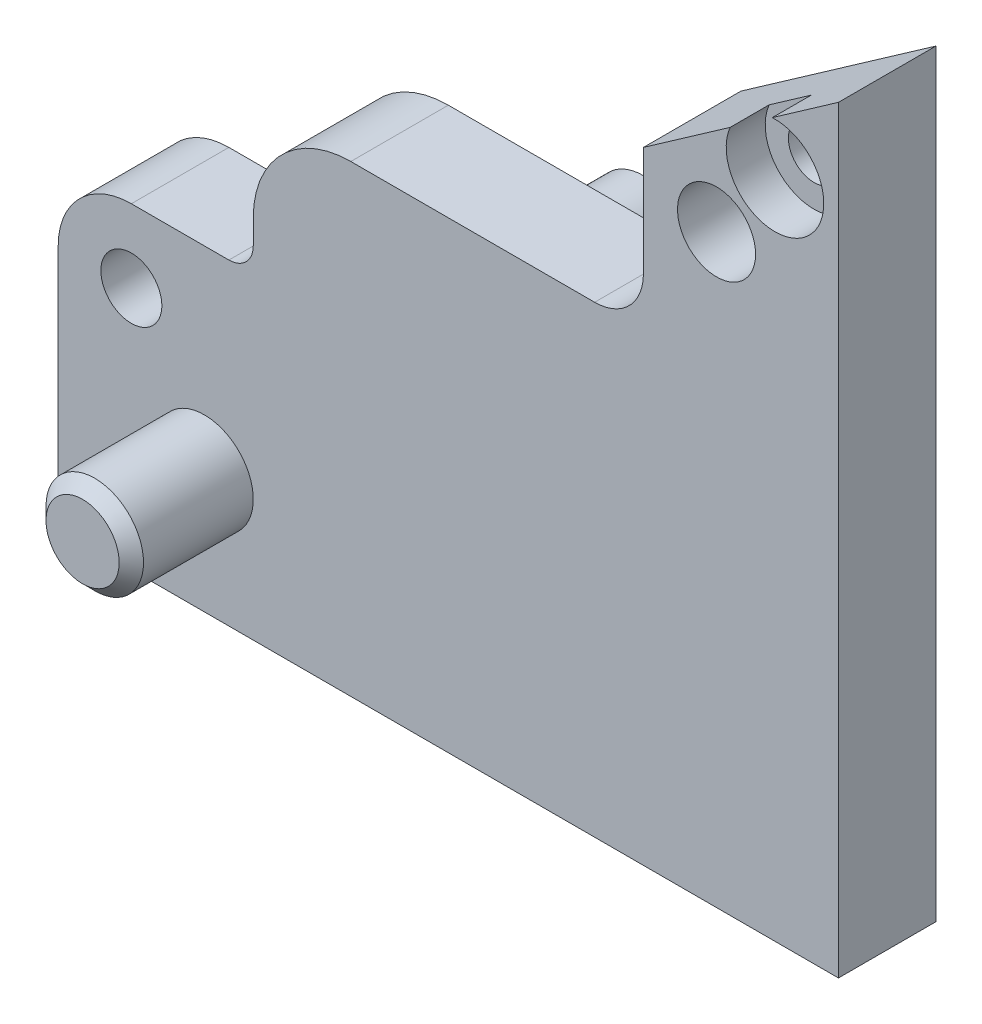
SolidWorks part; units mm, degrees
ref_plane "Front Plane" through (0, 0, 0) normal (0, 0, 1) x (1, 0, 0)
ref_plane "Top Plane" through (0, 0, 0) normal (0, 1, 0) x (1, 0, 0)
ref_plane "Right Plane" through (0, 0, 0) normal (1, 0, 0) x (0, 0, -1)
ref_plane "Plane1" through (0, 0, 0) normal (0, 0, -1) x (-1, 0, 0)
sketch "Sketch1" plane through (0, 0, 0) normal (0, 0, -1) x (-1, 0, 0)
  line L0 (0, 0) -> (0, 31.1017)
  line L1 (0, 31.1017) -> (-32, 31.1017)
  line L2 (-32, 31.1017) -> (-32, 0)
  line L3 (-32, 0) -> (0, 0)
extrude "Boss-Extrude1" add sketch "Sketch1" against normal blind 4
sketch "Sketch2" plane through (0, 0, 4) normal (0, 0, 1) x (1, 0, 0)
  line L0 (0, 13) -> (8, 13)
  line L1 (8, 13) -> (8, 31.1017)
  line L2 (8, 31.1017) -> (0, 31.1017)
  line L3 (0, 31.1017) -> (0, 13)
extrude "Cut-Extrude1" cut sketch "Sketch2" against normal through all
sketch "Sketch3" plane through (0, 0, 4) normal (0, 0, 1) x (1, 0, 0)
  line L0 (8, 19) -> (24, 19)
  line L1 (24, 19) -> (24, 31.1017)
  line L2 (24, 31.1017) -> (8, 31.1017)
  line L3 (8, 31.1017) -> (8, 19)
extrude "Cut-Extrude2" cut sketch "Sketch3" against normal through all
draft "Draft1" type of draft neutral plane draft angle 35 faces to draft 1 face at (28, 31.1017, 2) neutral plane through (32, 31.1017, 4) neutral plane normal (1, 0, 0) reverse direction yes parameters "D1"=35
ref_plane "Plane2" through (0, 5, 0) normal (0, -1, 0) x (1, 0, 0)
sketch "Sketch4" plane through (0, 5, 0) normal (0, -1, 0) x (1, 0, 0)
  line L0 (8, 9) -> (6, 9)
  line L1 (6, 9) -> (6, 4)
  line L2 (6, 4) -> (8, 4)
  line L3 (8, 4) -> (8, 9)
  line L4 (6, 9) -> (6, 4) construction
revolve "Revolve1" add sketch "Sketch4" angle 360 about L4
ref_plane "Plane3" through (0, 14, 0) normal (0, 1, 0) x (1, 0, 0)
sketch "Sketch5" plane through (0, 14, 0) normal (0, 1, 0) x (1, 0, 0)
  line L0 (17.5, 5) -> (15.5, 5)
  line L1 (15.5, 5) -> (15.5, 0)
  line L2 (15.5, 0) -> (17.5, 0)
  line L3 (17.5, 0) -> (17.5, 5)
  line L4 (15.5, 5) -> (15.5, 0) construction
revolve "Revolve2" add sketch "Sketch5" angle 360 about L4
hole_wizard "Ø3.2 (3.2) Diameter Hole1" positions "Sketch7" profile "Sketch6" hole size "Ø3.2" standard "ANSI Metric"
sketch "Sketch7" plane through (0, 0, 4) normal (0, 0, 1) x (1, 0, 0)
  point P0 (27, 24)
sketch "Sketch6" plane through (27, 24, 4) normal (1, 0, 0) x (0, -1, 0)
  line L0 (0, 0) -> (0, 9)
  line L1 (0, 9) -> (1.6, 9)
  line L2 (1.6, 9) -> (1.6, 0)
  line L5 (1.6, 0) -> (0, 0)
  line L11 (0, -6.35) -> (0, 107.95) construction
  dimension "Thru Hole Dia." = 3.2
  dimension "Thru Hole Depth" = 9
hole_wizard "Ø2.5 (2.5) Diameter Hole1" positions "Sketch9" profile "Sketch8" hole size "Ø2.5" standard "ANSI Metric"
sketch "Sketch9" plane through (0, 0, 0) normal (0, 0, -1) x (-1, 0, 0)
  point P0 (-3, 10)
sketch "Sketch8" plane through (3, 10, 0) normal (1, 0, 0) x (0, 1, 0)
  line L0 (0, 0) -> (0, 9)
  line L1 (0, 9) -> (1.25, 9)
  line L2 (1.25, 9) -> (1.25, 0)
  line L5 (1.25, 0) -> (0, 0)
  line L11 (0, -6.35) -> (0, 107.95) construction
  dimension "Thru Hole Dia." = 2.5
  dimension "Thru Hole Depth" = 9
hole_wizard "M4x0.7 Tapped Hole1" positions "Sketch11" profile "Sketch10" tap size "M4x0.7" standard "ANSI Metric"
sketch "Sketch11" plane through (0, 0, 4) normal (0, 0, 1) x (1, 0, 0)
  point P0 (29.396, 27.203)
sketch "Sketch10" plane through (29.396, 27.203, 4) normal (1, 0, 0) x (0, -1, 0)
  line L0 (0, 0) -> (0, 9)
  line L1 (0, 9) -> (1.05, 9)
  line L3 (1.05, 9) -> (1.05, 1.6)
  line L4 (1.05, 1.6) -> (2, 1.6)
  line L5 (2, 1.6) -> (2, 0)
  line L7 (2, 0) -> (0, 0)
  line L11 (0, -6.35) -> (0, 107.95) construction
  dimension "Thru Tap Drill Dia." = 2.1
  dimension "Thru Tap Drill Depth" = 9
  dimension "Thread Major Dia." = 4
  dimension "Thread Depth" = 1.6
hole_wizard "Ø2.5 (2.5) Diameter Hole2" positions "Sketch13" profile "Sketch12" hole size "Ø2.5" standard "ANSI Metric"
sketch "Sketch13" plane through (0, 0, 0) normal (0, -1, 0) x (-1, 0, 0)
  point P0 (-10, -2)
  point P1 (-19.5, -2)
  point P2 (-29, -2)
sketch "Sketch12" plane through (10, 0, 2) normal (1, 0, 0) x (0, 0, -1)
  line L0 (0, 0) -> (0, 8.2511)
  line L1 (0, 8.2511) -> (1.25, 7.5)
  line L2 (1.25, 7.5) -> (1.25, 0)
  line L5 (1.25, 0) -> (0, 0)
  line L10 (0, 8.2511) -> (-1.25, 7.5) construction
  line L11 (0, -6.35) -> (0, 107.95) construction
  dimension "Hole Dia." = 2.5
  dimension "Hole Depth" = 7.5
  dimension "Drill Angle" = 118
chamfer "Chamfer1" distance 0.5 angle 45 2 edges at (4, 5, 9) (17.5, 14, -5)
fillet "Fillet1" radius 1 1 edges at (8, 13, 2)
fillet "Fillet2" radius 2 1 edges at (24, 19, 2)
fillet "Fillet3" radius 3 1 edges at (0, 13, 2)
fillet "Fillet4" radius 4 1 edges at (8, 19, 2)
